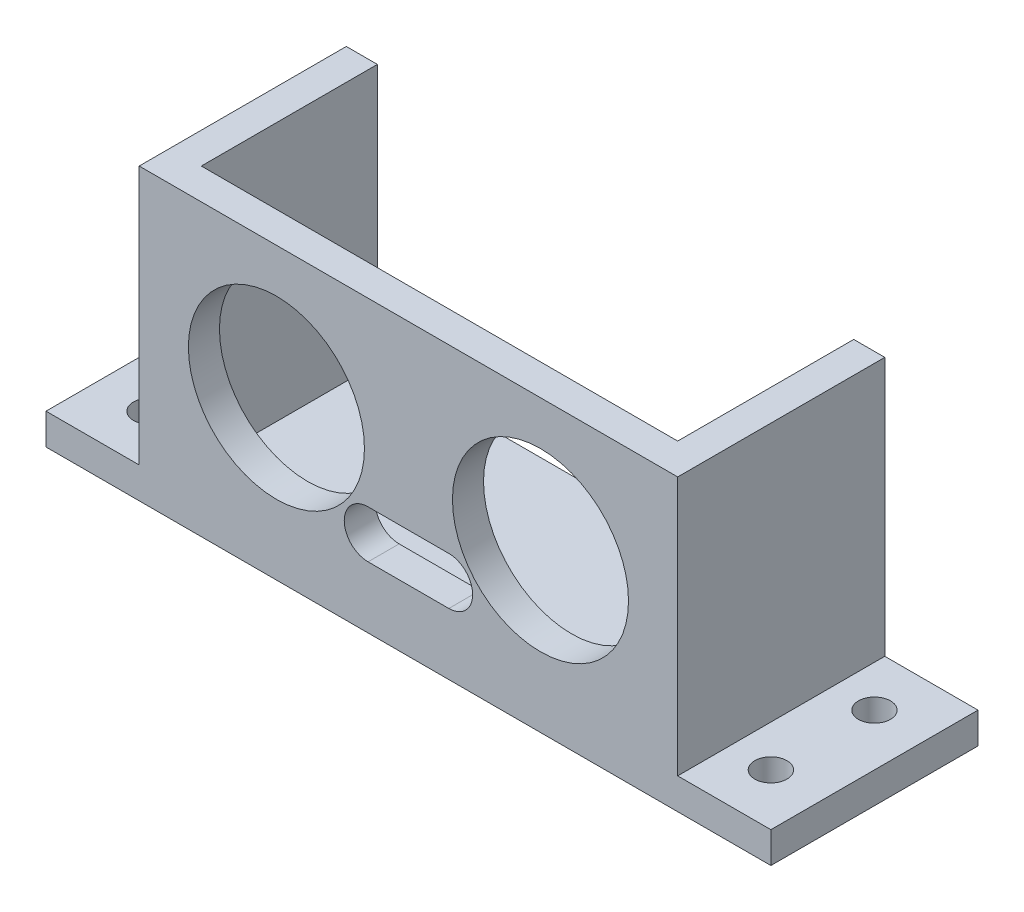
SolidWorks part; units mm, degrees
material "1060 Alloy"
ref_plane "Front Plane" through (0, 0, 0) normal (0, 0, 1) x (1, 0, 0)
ref_plane "Top Plane" through (0, 0, 0) normal (0, 1, 0) x (1, 0, 0)
ref_plane "Right Plane" through (0, 0, 0) normal (1, 0, 0) x (0, 0, -1)
sketch "Sketch1" plane through (0, 0, 0) normal (0, 1, 0) x (1, 0, 0)
  line L1 (-35, -10) -> (35, -10)
  line L2 (-35, -10) -> (-35, 10)
  line L3 (-35, 10) -> (35, 10)
  line L4 (35, -10) -> (35, 10)
  line L5 (0, 10) -> (0, -10) construction
  line L6 (-35, 0) -> (35, 0) construction
  circle A0 centre (-30, -5) radius 1.55
  circle A1 centre (30, -5) radius 1.55
  circle A2 centre (30, 5) radius 1.55
  circle A3 centre (-30, 5) radius 1.55
  point P0 (0, 0)
  dimension "D5" = 3.1
  dimension "D1" = 70
  dimension "D2" = 20
  dimension "D3" = 5
  dimension "D4" = 5
extrude "Boss-Extrude1" add sketch "Sketch1" along normal blind 3
sketch "Sketch2" plane through (0, 3, 0) normal (0, 1, 0) x (1, 0, 0)
  line L0 (-35, -10) -> (35, -10) construction
  line L1 (26, 10) -> (-26, 10)
  line L2 (26, 10) -> (26, -10)
  line L3 (26, -10) -> (-26, -10)
  line L4 (-26, 10) -> (-26, -10)
  line L5 (0, -10) -> (0, 10) construction
  line L6 (26, 0) -> (-26, 0) construction
  line L7 (-23, 10) -> (-23, -10)
  line L8 (23, 10) -> (23, -10)
  line L9 (26, -7) -> (-26, -7)
  point P0 (0, 0)
  line M5 (35, 10) -> (-35, 10)
  line M7 (-35, -10) -> (35, -10)
  dimension "D1" = 52
  dimension "D2" = 3
  dimension "D3" = 3
  dimension "D4" = 3
extrude "Boss-Extrude2" add sketch "Sketch2" along normal blind 25 contours L9 L7 L1 L4 | L7 L9 L4 M7 | L8 L9 L7 L3 | L2 L9 L8 M7 | L9 L2 L8 M5
sketch "Sketch3" plane through (0, 0, 10) normal (0, 0, 1) x (1, 0, 0)
  line L0 (-35, 0) -> (35, 0) construction
  line L1 (22.75, 25.5) -> (-22.75, 25.5) construction
  line L2 (22.75, 25.5) -> (22.75, 5) construction
  line L3 (22.75, 5) -> (-22.75, 5) construction
  line L4 (-22.75, 25.5) -> (-22.75, 5) construction
  line L5 (0, 5) -> (0, 25.5) construction
  line L6 (22.75, 15.25) -> (-22.75, 15.25) construction
  line L7 (-3.9, 8.25) -> (3.9, 8.25) construction
  line L8 (-3.9, 10.55) -> (3.9, 10.55)
  line L9 (-3.9, 5.95) -> (3.9, 5.95)
  circle A0 centre (-12.75, 15.25) radius 8.5
  circle A1 centre (12.75, 15.25) radius 8.5
  arc A2 (-3.9, 10.55) -> (-3.9, 5.95) centre (-3.9, 8.25) ccw
  arc A3 (3.9, 5.95) -> (3.9, 10.55) centre (3.9, 8.25) ccw
  point P0 (0, 15.25)
  point P12 (0, 8.25)
  point P17 (0, 8.1607)
  dimension "D3" = 17
  dimension "D1" = 20.5
  dimension "D2" = 45.5
  dimension "D5" = 5
  dimension "D6" = 4.6
  dimension "D4" = 10
  dimension "D8" = 3.25
  dimension "D7" = 7.8
extrude "Cut-Extrude1" cut sketch "Sketch3" against normal blind 3
equation "\"D4@Sketch3\"=1.5+\"D3@Sketch3\"/2"
